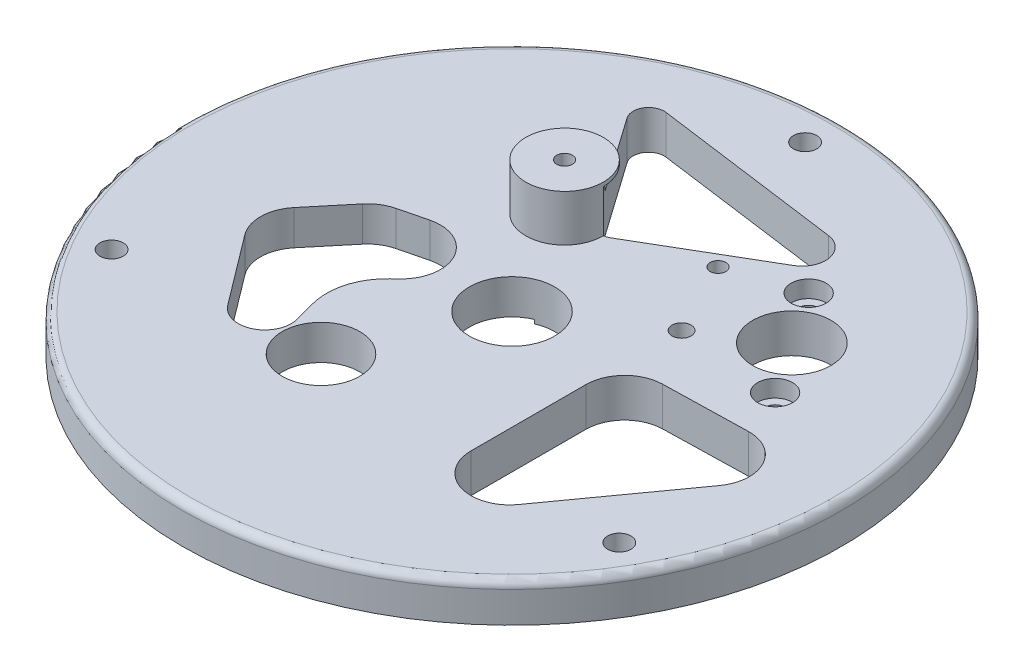
SolidWorks part; units mm, degrees
ref_plane "Front Plane" through (0, 0, 0) normal (0, 0, 1) x (1, 0, 0)
ref_plane "Top Plane" through (0, 0, 0) normal (0, 1, 0) x (1, 0, 0)
ref_plane "Right Plane" through (0, 0, 0) normal (1, 0, 0) x (0, 0, -1)
sketch "Sketch1" plane through (0, 0, 0) normal (0, 1, 0) x (1, 0, 0)
  circle A0 centre (0, 0) radius 42.5
  circle A9 centre (-7.5739, -17.0603) radius 5
  dimension "D1" = 85
  dimension "D5" = 10
  dimension "D6" = 18.666
extrude "Boss-Extrude1" add sketch "Sketch1" along normal blind 5
sketch "Sketch2" plane through (0, 5, 0) normal (0, 1, 0) x (1, 0, 0)
  line L0 (26.0308, 7.8992) -> (17.0876, 21.1664) construction
  line L1 (26.0308, 7.8992) -> (13.0624, 8.8052) construction
  line L2 (13.0624, 8.8052) -> (17.0876, 21.1664) construction
  line L3 (13.0624, 8.8052) -> (21.5592, 14.5328) construction
  circle A0 centre (26.0308, 7.8992) radius 1.2
  circle A1 centre (17.0876, 21.1664) radius 1.2
  circle A2 centre (13.0624, 8.8052) radius 1.225
  circle A3 centre (21.5592, 14.5328) radius 5.05
  circle A4 centre (8.3208, 18.2484) radius 1.015
  circle A5 centre (21.5592, 14.5328) radius 13.75 construction
  circle A6 centre (0, 0) radius 30 construction
  circle A7 centre (8.3208, 18.2484) radius 11.25 construction
  point P9 (21.5592, 14.5328)
  dimension "D1" = 2.4
  dimension "D2" = 10.1
  dimension "D3" = 2.45
  dimension "D7" = 2.03
  dimension "D9" = 60
  dimension "D10" = 22.5
  dimension "D4" = 16
  dimension "D5" = 13
  dimension "D6" = 26
  dimension "D8" = 13.75
extrude "Cut-Extrude1" cut sketch "Sketch2" against normal blind 10
sketch "Sketch4" plane through (0, 5, 0) normal (0, 1, 0) x (1, 0, 0)
  circle A0 centre (0, 0) radius 31 construction
  dimension "D1" = 62
sketch "Sketch5" plane through (0, 5, 0) normal (0, 1, 0) x (1, 0, 0)
  line L0 (-7.5531, 14.3315) -> (0, 0) construction
  circle A0 centre (-7.5531, 14.3315) radius 5
  circle A1 centre (8.3208, 18.2484) radius 1 construction
  circle A2 centre (-7.5531, 14.3315) radius 1.015
  circle A3 centre (-7.5531, 14.3315) radius 14 construction
  dimension "D2" = 10
  dimension "D3" = 2.03
  dimension "D4" = 28
  dimension "D1" = 16.35
  dimension "D5" = 16.2
extrude "Boss-Extrude2" add sketch "Sketch5" along normal blind 6
sketch "Sketch9" plane through (0, 0, 0) normal (0, -1, 0) x (1, 0, 0)
  circle A0 centre (8.3208, -18.2484) radius 2.3573
extrude "Boss-Extrude4" add sketch "Sketch9" against normal blind 1
fillet "Fillet1" radius 1 1 edges at (0, 5, 42.5)
sketch "Sketch10" plane through (0, 5, 0) normal (0, 1, 0) x (1, 0, 0)
  line L0 (-32.7358, -18.9) -> (0, 0) construction
  line L1 (0, 37.8) -> (0, 0) construction
  line L2 (32.7358, -18.9) -> (0, 0) construction
  circle A0 centre (0, 37.8) radius 1.5
  circle A1 centre (-32.7358, -18.9) radius 1.5
  circle A2 centre (32.7358, -18.9) radius 1.5
  dimension "D2" = 3
  dimension "D3" = 120
  dimension "D1" = 37.8
  dimension "D4" = 120
extrude "Cut-Extrude3" cut sketch "Sketch10" against normal blind 16 and the other way blind 2.2
sketch "Sketch12" plane through (0, 0, 0) normal (0, -1, 0) x (1, 0, 0)
  line L0 (-21.3138, 24.7621) -> (-34.5388, 1.8558)
  line L1 (-32.7087, -4.9744) -> (-14.0892, -15.7244)
  line L2 (-7.259, -13.8942) -> (5.966, 9.0121)
  line L3 (5.966, 9.0121) -> (-21.3138, 24.7621) construction
  line L4 (-7.6739, 16.8871) -> (-7.5739, 17.0603) construction
  line L5 (-32.7358, 18.9) -> (-36.8061, 21.25) construction
  line L6 (-26.7077, 15.4197) -> (-32.7358, 18.9) construction
  line L7 (-35.4958, 23.5194) -> (-39.334, 16.8715) construction
  arc A0 (-21.3138, 24.7621) -> (5.966, 9.0121) centre (-7.6739, 16.8871) cw
  arc A1 (-7.259, -13.8942) -> (-14.0892, -15.7244) centre (-11.5892, -11.3942) cw
  arc A2 (-34.5388, 1.8558) -> (-32.7087, -4.9744) centre (-30.2087, -0.6442) ccw
  circle A3 centre (-7.5739, 17.0603) radius 4.1018 construction
  circle A4 centre (-7.5739, 17.0603) radius 5 construction
  circle A5 centre (0, 0) radius 42.5 construction
  point P4 (0.2011, 30.527)
  point P9 (-9.759, -18.2244)
  point P12 (-37.0388, -2.4744)
  dimension "D3" = 5
  dimension "D4" = 0.2
  dimension "D1" = 47.2
  dimension "D2" = 31.5
extrude "Cut-Extrude6" cut sketch "Sketch12" against normal blind 0.5
sketch "Sketch13" plane through (0, 5, 0) normal (0, 1, 0) x (1, 0, 0)
  line L0 (32.8168, -6.0717) -> (21.985, -21.1386)
  line L1 (12.9252, -18.2178) -> (12.9317, -3.4072)
  line L2 (17.8133, 1.5892) -> (28.6387, 1.8455)
  arc A0 (21.985, -21.1386) -> (12.9252, -18.2178) centre (17.9252, -18.22) cw
  arc A1 (17.8133, 1.5892) -> (12.9317, -3.4072) centre (17.9317, -3.4094) ccw
  arc A2 (28.6387, 1.8455) -> (32.8168, -6.0717) centre (28.7571, -3.1531) cw
  dimension "D1" = 5
extrude "Cut-Extrude7" cut sketch "Sketch13" against normal blind 10
sketch "Sketch15" plane through (0, 0.5, 0) normal (0, -1, 0) x (1, 0, 0)
  line L0 (-4.4541, -15.187) -> (-14.1901, -29.0283)
  line L1 (-12.2862, -32.1609) -> (11.9263, -28.8867)
  line L2 (13.0439, -23.3011) -> (-1.8082, -14.6114)
  arc A0 (-4.4541, -15.187) -> (-1.8082, -14.6114) centre (-2.8182, -16.3376) cw
  arc A1 (-12.2862, -32.1609) -> (-14.1901, -29.0283) centre (-12.5542, -30.1789) cw
  arc A2 (11.9263, -28.8867) -> (13.0439, -23.3011) centre (11.5226, -25.9013) ccw
  dimension "D1" = 2
extrude "Cut-Extrude8" cut sketch "Sketch15" against normal blind 10 and the other way blind 10
sketch "Sketch16" plane through (0, 0.5, 0) normal (0, -1, 0) x (1, 0, 0)
  line L0 (-12.9842, 14.7056) -> (-13.7197, 11.9588)
  line L1 (-11.5496, 4.2419) -> (-10.8428, 3.5689)
  line L2 (-15.4939, -4.9052) -> (-19.0041, -4.0349)
  line L3 (-21.6454, -2.3787) -> (-25.6533, 2.4414)
  line L4 (-25.8003, 8.6495) -> (-19.0121, 17.6471)
  arc A0 (-25.6533, 2.4414) -> (-25.8003, 8.6495) centre (-21.8088, 5.6382) cw
  arc A1 (-19.0041, -4.0349) -> (-21.6454, -2.3787) centre (-17.8008, 0.8181) cw
  arc A2 (-15.4939, -4.9052) -> (-10.8428, 3.5689) centre (-14.2907, -0.0522) ccw
  arc A3 (-13.7197, 11.9588) -> (-11.5496, 4.2419) centre (-6.1357, 9.9279) ccw
  arc A4 (-12.9842, 14.7056) -> (-19.0121, 17.6471) centre (-16.2845, 15.5894) ccw
  dimension "D1" = 5
extrude "Cut-Extrude9" cut sketch "Sketch16" against normal blind 10 and the other way blind 10
sketch "Sketch17" plane through (0, 0.5, 0) normal (0, -1, 0) x (1, 0, 0)
  circle A0 centre (0, 0) radius 5.5
  dimension "D1" = 11
extrude "Cut-Extrude10" cut sketch "Sketch17" against normal blind 10 and the other way blind 10
sketch "Sketch18" plane through (0, 5, 0) normal (0, 1, 0) x (1, 0, 0)
  circle A0 centre (17.0876, 21.1664) radius 2.25
  circle A1 centre (26.0308, 7.8992) radius 2.25
  dimension "D1" = 4.5
extrude "Cut-Extrude11" cut sketch "Sketch18" against normal blind 2.2
